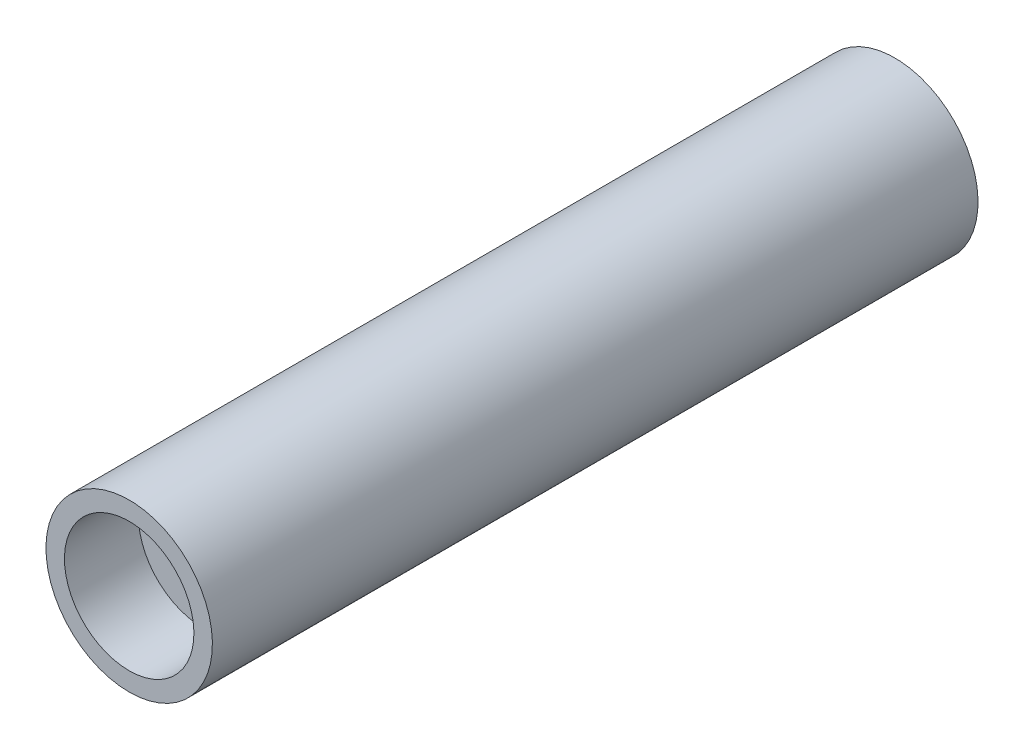
SolidWorks part; units mm, degrees
material "Brass"
ref_plane "Front Plane" through (0, 0, 0) normal (0, 0, 1) x (1, 0, 0)
ref_plane "Top Plane" through (0, 0, 0) normal (0, 1, 0) x (1, 0, 0)
ref_plane "Right Plane" through (0, 0, 0) normal (1, 0, 0) x (0, 0, -1)
sketch "Sketch1" plane through (0, 0, 0) normal (1, 0, 0) x (0, 0, -1)
  line L0 (-16.93, 0) -> (16.93, 0) construction
  line L1 (0, 2.082) -> (0, -2.082) construction
  line L2 (16.7, 3.5) -> (20.7, 3.5)
  line L3 (-20.7, 4.5) -> (20.7, 4.5)
  line L4 (-20.7, 4.5) -> (-20.7, 3.5)
  line L5 (-20.7, 3.5) -> (-16.7, 3.5)
  line L6 (20.7, 4.5) -> (20.7, 3.5)
  line L7 (-20.7, 4.5) -> (20.7, 3.5) construction
  line L8 (-20.7, 3.5) -> (20.7, 4.5) construction
  line L9 (-16.7, 3.5) -> (-16.7, 2)
  line L10 (-16.7, 2) -> (16.7, 2)
  line L11 (16.7, 3.5) -> (16.7, 2)
  point P0 (0, 4)
  point P3 (0, 0)
  point P6 (0, 0)
  point P15 (20.7, 4)
  dimension "D1" = 41.4
  dimension "D2" = 4
  dimension "D3" = 4
  dimension "D4" = 7
  dimension "D5" = 2
  dimension "D6" = 4.5
revolve "Revolve1" add sketch "Sketch1" angle 360 about L0
scale "Scale1" bodies to scale 101 scale about centroid uniform scaling yes scale factor 0.6
